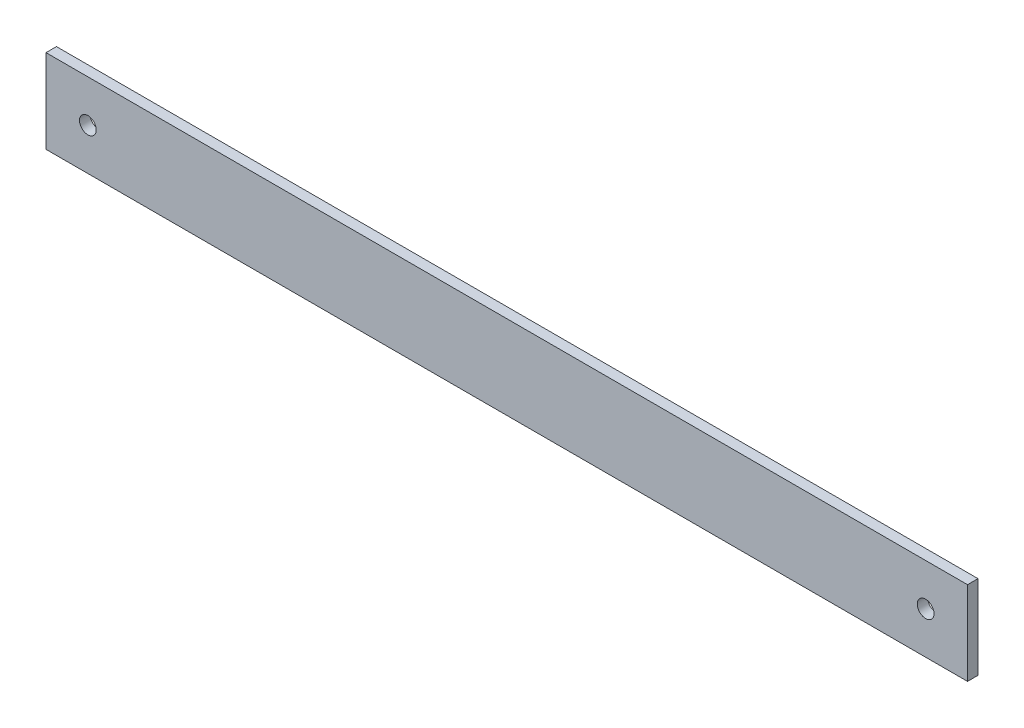
SolidWorks part; units mm, degrees
ref_plane "Front Plane" through (0, 0, 0) normal (0, 0, 1) x (1, 0, 0)
ref_plane "Top Plane" through (0, 0, 0) normal (0, 1, 0) x (1, 0, 0)
ref_plane "Right Plane" through (0, 0, 0) normal (1, 0, 0) x (0, 0, -1)
sketch "Sketch1" plane through (0, 0, 0) normal (0, 0, 1) x (1, 0, 0)
  line L0 (0, 0) -> (0, -85.935) construction
  line L1 (-220, 20) -> (220, 20)
  line L2 (-220, 20) -> (-220, -20)
  line L3 (-220, -20) -> (220, -20)
  line L4 (220, 20) -> (220, -20)
  line L5 (-220, 20) -> (220, -20) construction
  line L6 (-220, -20) -> (220, 20) construction
  circle A0 centre (200, 0) radius 4
  circle A1 centre (-200, 0) radius 4
  point P0 (0, 0)
  dimension "D3" = 20
  dimension "D1" = 440
  dimension "D2" = 40
extrude "Boss-Extrude1" add sketch "Sketch1" along normal blind 5
